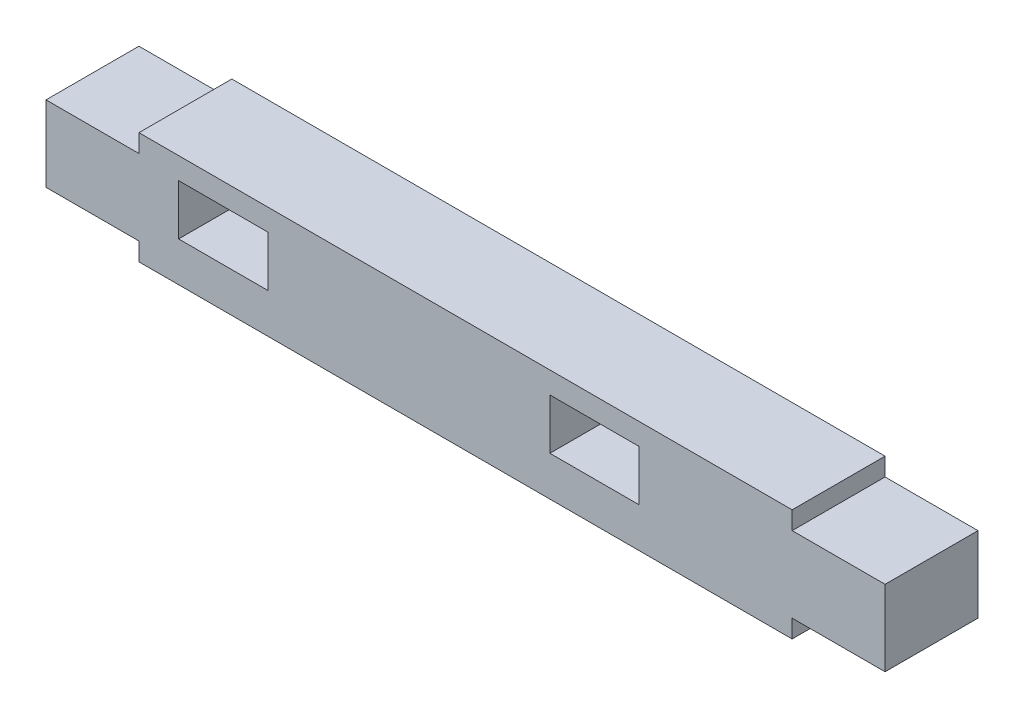
SolidWorks part; units mm, degrees
ref_plane "Front Plane" through (0, 0, 0) normal (0, 0, 1) x (1, 0, 0)
ref_plane "Top Plane" through (0, 0, 0) normal (0, 1, 0) x (1, 0, 0)
ref_plane "Right Plane" through (0, 0, 0) normal (1, 0, 0) x (0, 0, -1)
sketch "Sketch1" plane through (0, 0, 0) normal (0, 0, 1) x (1, 0, 0)
  line L0 (-18, 6) -> (18, 6) construction
  line L1 (0, -55) -> (0, 55) construction
  line L2 (18, 6) -> (18, 5) construction
  line L3 (18, 5) -> (23.15, 5) construction
  line L4 (23.15, 5) -> (23.15, 1) construction
  line L5 (23.15, 1) -> (18, 1) construction
  line L6 (18, 1) -> (18, 0) construction
  line L7 (55, 0) -> (-55, 0) construction
  line L8 (18, 0) -> (-18, 0) construction
  line L9 (0, 22.3415) -> (0, -9.0349) construction
  line L10 (-18, 1) -> (-18, 0) construction
  line L11 (-23.15, 1) -> (-18, 1) construction
  line L12 (-23.15, 5) -> (-23.15, 1) construction
  line L13 (-18, 5) -> (-23.15, 5) construction
  line L14 (-18, 6) -> (-18, 5) construction
  line L15 (-18.1, 6.1) -> (18.1, 6.1)
  line L16 (18.1, 6.1) -> (18.1, 5.1)
  line L17 (18.1, 5.1) -> (23.25, 5.1)
  line L18 (23.25, 5.1) -> (23.25, 0.9)
  line L19 (23.25, 0.9) -> (18.1, 0.9)
  line L20 (18.1, 0.9) -> (18.1, -0.1)
  line L21 (18.1, -0.1) -> (-18.1, -0.1)
  line L22 (-18.1, 0.9) -> (-18.1, -0.1)
  line L23 (-23.25, 0.9) -> (-18.1, 0.9)
  line L24 (-23.25, 5.1) -> (-23.25, 0.9)
  line L25 (-18.1, 5.1) -> (-23.25, 5.1)
  line L26 (-18.1, 6.1) -> (-18.1, 5.1)
  point P16 (0, 0)
  point P21 (0, 6)
  dimension "D1" = 6
  dimension "D2" = 4
  dimension "D3" = 36
  dimension "D4" = 5.15
  dimension "D5" = 0.1
extrude "Boss-Extrude1" add sketch "Sketch1" along normal blind 5.15
sketch "Sketch3" plane through (0, 0, 5.15) normal (0, 0, 1) x (1, 0, 0)
  line L0 (0, 8.3794) -> (0, -6.0522) construction
  line L1 (4.675, 4.9) -> (9.625, 4.9)
  line L2 (-23.15, 3) -> (23.15, 3) construction
  line L3 (-23.15, 5) -> (-23.15, 1) construction
  line L4 (23.15, 1) -> (23.15, 5) construction
  line L5 (18, 0) -> (18, 1) construction
  line L6 (4.575, 5) -> (9.725, 5) construction
  line L7 (4.575, 5) -> (4.575, 2) construction
  line L8 (4.575, 2) -> (9.725, 2) construction
  line L9 (9.725, 5) -> (9.725, 2) construction
  line L10 (-18, 6) -> (-18, 5) construction
  line L11 (-16, 5) -> (-10.85, 5) construction
  line L12 (-16, 5) -> (-16, 2) construction
  line L13 (-16, 2) -> (-10.85, 2) construction
  line L14 (-10.85, 5) -> (-10.85, 2) construction
  line L15 (9.625, 4.9) -> (9.625, 2.1)
  line L16 (4.675, 2.1) -> (9.625, 2.1)
  line L17 (4.675, 4.9) -> (4.675, 2.1)
  line L18 (-15.9, 4.9) -> (-10.95, 4.9)
  line L19 (-10.95, 4.9) -> (-10.95, 2.1)
  line L20 (-15.9, 2.1) -> (-10.95, 2.1)
  line L21 (-15.9, 4.9) -> (-15.9, 2.1)
  dimension "D1" = 5.15
  dimension "D2" = 3
  dimension "D3" = 8.275
  dimension "D4" = 2
  dimension "D5" = 0.1
extrude "Cut-Extrude1" cut sketch "Sketch3" against normal through all
